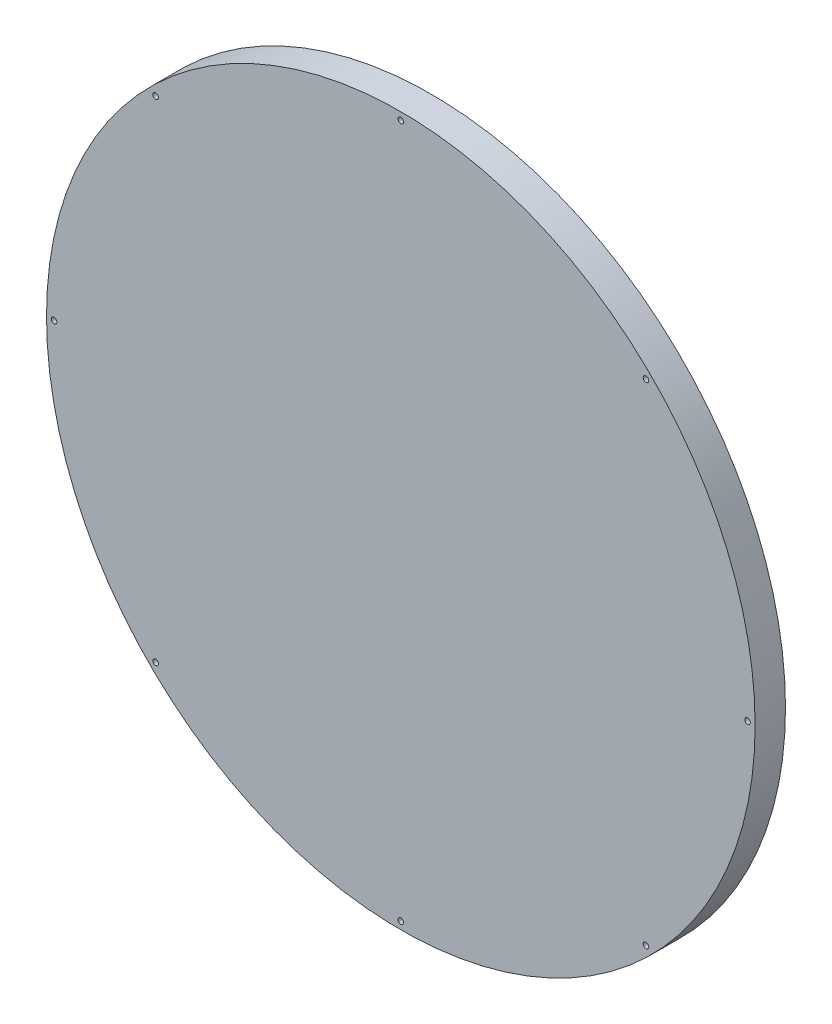
SolidWorks part; units mm, degrees
material "6061-T6 (SS)"
ref_plane "Front" through (0, 0, 0) normal (0, 0, 1) x (1, 0, 0)
ref_plane "Top" through (0, 0, 0) normal (0, 1, 0) x (1, 0, 0)
ref_plane "Right" through (0, 0, 0) normal (1, 0, 0) x (0, 0, -1)
sketch "Sketch1" plane through (0, 0, 0) normal (0, 0, 1) x (1, 0, 0)
  circle A0 centre (0, 0) radius 140
extrude "Boss-Extrude1" add sketch "Sketch1" along normal blind 12
hole_wizard "CSK for M2 Flat Head Machine Screw1" positions "Sketch2" profile "Sketch3" countersink size "M2" standard "ANSI Metric" end condition through all
sketch "Sketch2" plane through (0, 0, 0) normal (0, 0, -1) x (-1, 0, 0)
  point P0 (0, 137)
  point P2 (137, 0)
  point P4 (0, -137)
  point P6 (-137, 0)
  point P9 (-137, 0)
  point P16 (-96.874, 96.874)
  point P18 (96.874, 96.874)
  point P20 (96.874, -96.874)
  point P22 (-96.874, -96.874)
sketch "Sketch3" plane through (0, 137, 0) normal (1, 0, 0) x (0, 1, 0)
  line L0 (0, 0) -> (0, 12)
  line L1 (0, 12) -> (1.1, 12)
  line L2 (1.1, 12) -> (1.1, 1.1)
  line L3 (1.1, 1.1) -> (2.2, 0)
  line L5 (2.2, 0) -> (0, 0)
  line L6 (-1.1, 1.1) -> (-2.2, 0) construction
  line L11 (0, -6.35) -> (0, 107.95) construction
  dimension "Thru Hole Dia." = 2.2
  dimension "Thru Hole Depth" = 12
  dimension "Near C'Sink Dia." = 4.4
  dimension "Near C'Sink Angle" = 90
